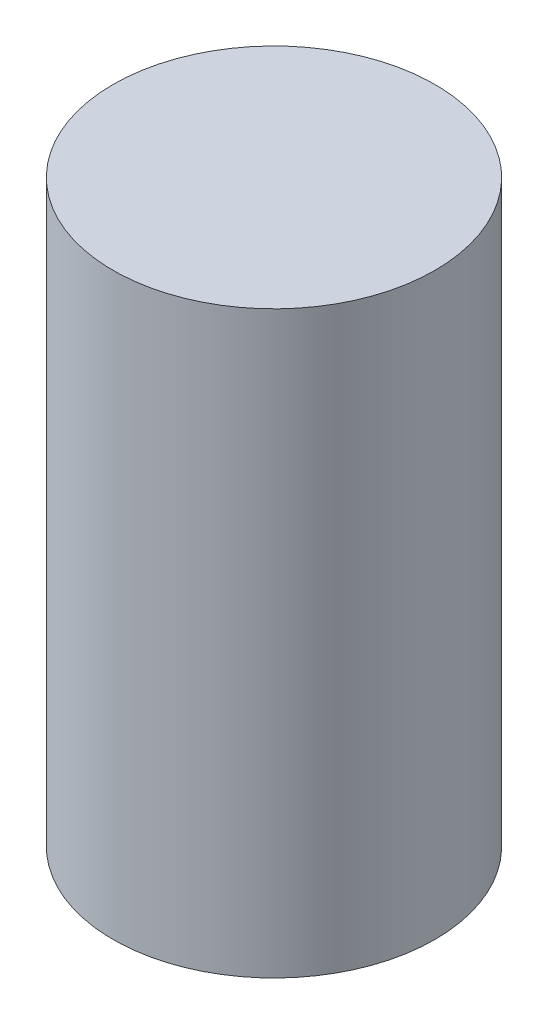
SolidWorks part; units mm, degrees
ref_plane "Front Plane" through (0, 0, 0) normal (0, 0, 1) x (1, 0, 0)
ref_plane "Top Plane" through (0, 0, 0) normal (0, 1, 0) x (1, 0, 0)
ref_plane "Right Plane" through (0, 0, 0) normal (1, 0, 0) x (0, 0, -1)
sketch "Sketch1" plane through (0, 0, 0) normal (0, 0, 1) x (1, 0, 0)
  line L0 (0, 31.5) -> (0, 48.9622) construction
  line L1 (-17.5, 31.5) -> (0, 31.5)
  line L2 (-17.5, 31.5) -> (-17.5, -31.5)
  line L3 (-17.5, -31.5) -> (0, -31.5)
  line L4 (0, 31.5) -> (0, -31.5)
  point P5 (0, 0)
  dimension "D1" = 63
  dimension "D2" = 35
revolve "Revolve1" add sketch "Sketch1" angle 360 about L0
